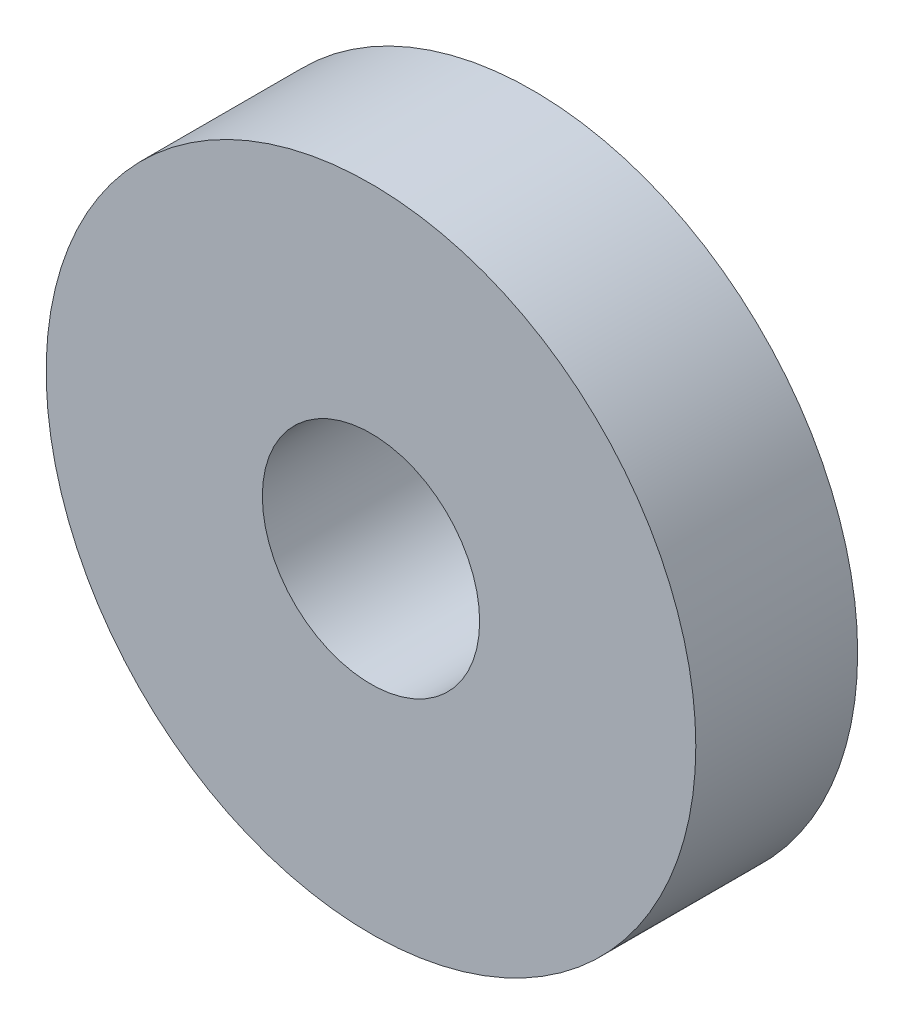
SolidWorks part; units mm, degrees
ref_plane "Front Plane" through (0, 0, 0) normal (0, 0, 1) x (1, 0, 0)
ref_plane "Top Plane" through (0, 0, 0) normal (0, 1, 0) x (1, 0, 0)
ref_plane "Right Plane" through (0, 0, 0) normal (1, 0, 0) x (0, 0, -1)
sketch "Sketch1" plane through (0, 0, 0) normal (0, 0, 1) x (1, 0, 0)
  circle A0 centre (0, 0) radius 2.3876
  circle A1 centre (0, 0) radius 7.1374
  dimension "ID" = 4.7752
  dimension "OD" = 14.2748
extrude "Extrude1" add sketch "Sketch1" against normal blind 3.556
